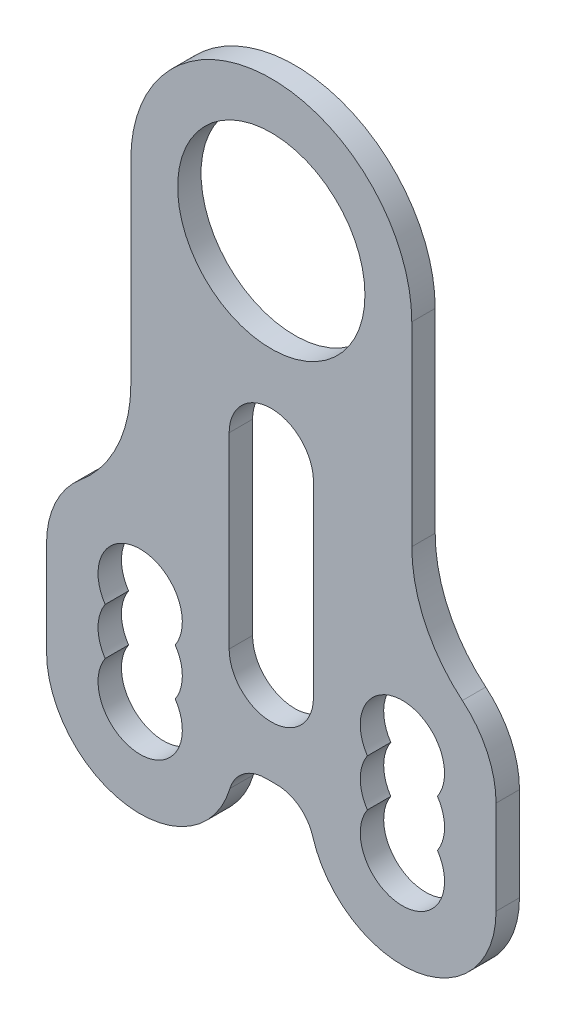
SolidWorks part; units mm, degrees
material "AISI 304"
ref_plane "前视基准面" through (0, 0, 0) normal (0, 0, 1) x (1, 0, 0)
ref_plane "上视基准面" through (0, 0, 0) normal (0, 1, 0) x (1, 0, 0)
ref_plane "右视基准面" through (0, 0, 0) normal (1, 0, 0) x (0, 0, -1)
sketch "草图1" plane through (0, 0, 0) normal (0, 0, 1) x (1, 0, 0)
  line L0 (0, 0) -> (0, -60) construction
  line L1 (14, -60) -> (-14, -60) construction
  line L2 (-14, -60) -> (-14, -50) construction
  line L3 (-14, -50) -> (-14, -40) construction
  line L4 (-24, -40) -> (-24, -50)
  line L6 (-15, 0) -> (-15, -20.7906)
  line L7 (-0.5836, -50) -> (0.5836, -50)
  line L8 (15, 0) -> (15, -20.7906)
  line L9 (14, -50) -> (14, -40) construction
  line L10 (14, -60) -> (14, -50) construction
  line L11 (24, -40) -> (24, -50)
  line L12 (0, -40) -> (0, -20) construction
  line L13 (-4.5, -20) -> (-4.5, -40)
  line L14 (4.5, -20) -> (4.5, -40)
  circle A0 centre (0, 0) radius 10
  arc A1 (15, 0) -> (-15, 0) centre (0, 0) ccw
  arc A2 (-24, -50) -> (-4.4169, -52.8571) centre (-14, -50) ccw
  arc A3 (-17.7417, -47.5) -> (-10.2583, -47.5) centre (-14, -50) ccw
  arc A4 (-10.2583, -42.5) -> (-17.7417, -42.5) centre (-14, -40) ccw
  arc A5 (-17.7417, -42.5) -> (-17.7417, -47.5) centre (-14, -45) ccw
  arc A6 (-10.2583, -47.5) -> (-10.2583, -42.5) centre (-14, -45) ccw
  arc A7 (-20.4, -32.3163) -> (-24, -40) centre (-14, -40) ccw
  arc A8 (-20.4, -32.3163) -> (-15, -20.7906) centre (-30, -20.7906) ccw
  arc A9 (20.4, -32.3163) -> (15, -20.7906) centre (30, -20.7906) cw
  arc A10 (20.4, -32.3163) -> (24, -40) centre (14, -40) cw
  arc A11 (10.2583, -47.5) -> (10.2583, -42.5) centre (14, -45) cw
  arc A12 (17.7417, -42.5) -> (17.7417, -47.5) centre (14, -45) cw
  arc A13 (10.2583, -42.5) -> (17.7417, -42.5) centre (14, -40) cw
  arc A14 (17.7417, -47.5) -> (10.2583, -47.5) centre (14, -50) cw
  arc A15 (24, -50) -> (4.4169, -52.8571) centre (14, -50) cw
  arc A16 (4.4169, -52.8571) -> (0.5836, -50) centre (0.5836, -54) ccw
  arc A17 (-4.4169, -52.8571) -> (-0.5836, -50) centre (-0.5836, -54) cw
  arc A18 (-4.5, -40) -> (4.5, -40) centre (0, -40) ccw
  arc A19 (4.5, -20) -> (-4.5, -20) centre (0, -20) ccw
  point P36 (0, -50)
  point P37 (4, -50)
  point P40 (-4, -50)
  dimension "D1" = 15
  dimension "D2" = 4
extrude "凸台-拉伸1" add sketch "草图1" along normal blind 2.5
